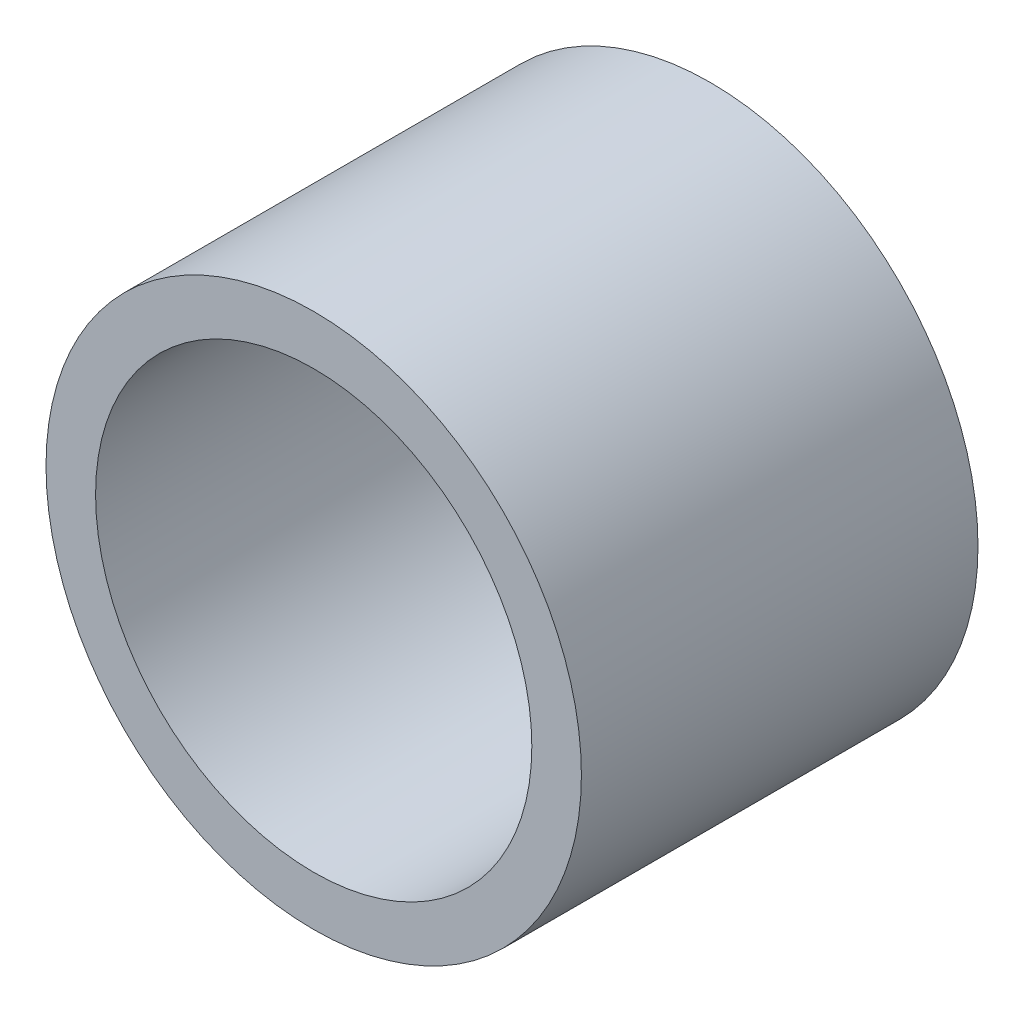
SolidWorks part; units mm, degrees
ref_plane "Front Plane" through (0, 0, 0) normal (0, 0, 1) x (1, 0, 0)
ref_plane "Top Plane" through (0, 0, 0) normal (0, 1, 0) x (1, 0, 0)
ref_plane "Right Plane" through (0, 0, 0) normal (1, 0, 0) x (0, 0, -1)
sketch "Sketch1" plane through (0, 0, 0) normal (0, 0, 1) x (1, 0, 0)
  circle A0 centre (0, 0) radius 5.5
  circle A1 centre (0, 0) radius 6.75
  dimension "D1" = 11
  dimension "D2" = 1.25
extrude "Boss-Extrude1" add sketch "Sketch1" along normal blind 10
